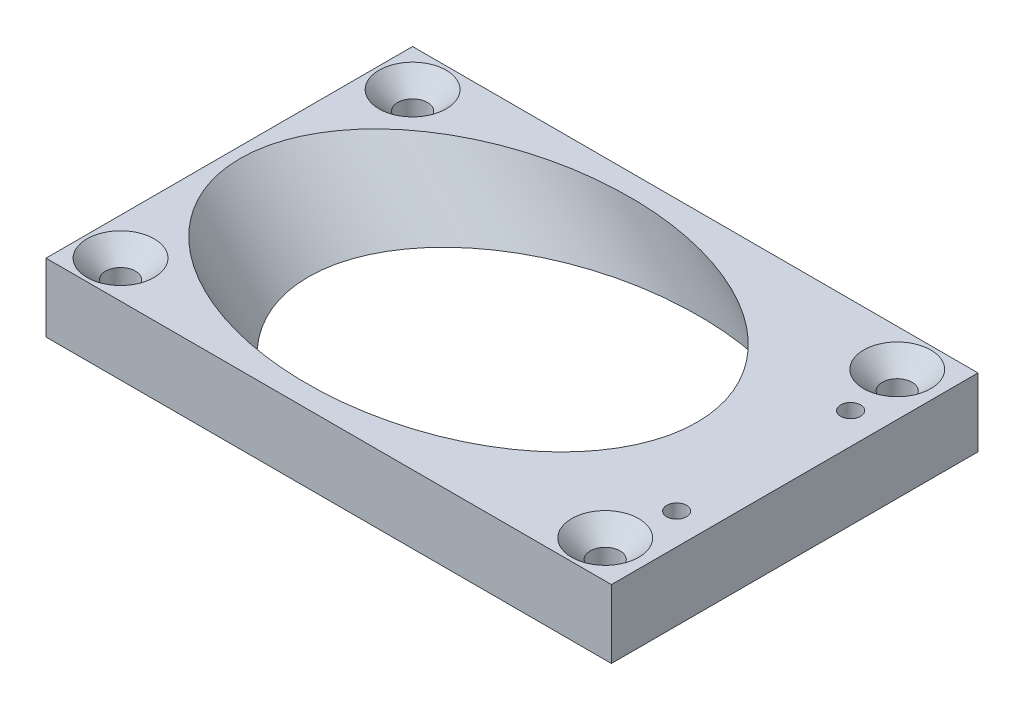
SolidWorks part; units mm, degrees
material "7075-T6 (SN)"
ref_plane "Front Plane" through (0, 0, 0) normal (0, 0, 1) x (1, 0, 0)
ref_plane "Top Plane" through (0, 0, 0) normal (0, 1, 0) x (1, 0, 0)
ref_plane "Right Plane" through (0, 0, 0) normal (1, 0, 0) x (0, 0, -1)
sketch "Sketch1" plane through (0, 0, 0) normal (0, 1, 0) x (1, 0, 0)
  line L1 (-22.75, -14.75) -> (22.75, -14.75)
  line L2 (-22.75, -14.75) -> (-22.75, 14.75)
  line L3 (-22.75, 14.75) -> (22.75, 14.75)
  line L4 (22.75, -14.75) -> (22.75, 14.75)
  line L5 (-22.75, -14.75) -> (22.75, 14.75) construction
  line L6 (-22.75, 14.75) -> (22.75, -14.75) construction
  point P0 (0, 0)
  dimension "D1" = 45.5
  dimension "D2" = 29.5
extrude "Boss-Extrude1" add sketch "Sketch1" along normal blind 5.5
ref_plane "Plane1" through (-14.125, 14.125, 0) normal (-0.7071, 0.7071, 0) x (0, 0, 1)
sketch "Sketch2" plane through (-14.125, 14.125, 0) normal (-0.7071, 0.7071, 0) x (0, 0, 1)
  line L0 (-14.75, -16.0867) -> (14.75, -16.0867) construction
  circle A0 centre (0, 1.4133) radius 13
  dimension "D1" = 26
  dimension "D2" = 17.5
extrude "Cut-Extrude1" cut sketch "Sketch2" against normal up to next
hole_wizard "CSK for M2 Countersunk Flat Head Screw1" positions "Sketch3" profile "Sketch4" countersink size "M2" standard "DIN" end condition through all
sketch "Sketch3" plane through (0, 5.5, 0) normal (0, 1, 0) x (1, 0, 0)
  line L1 (-19.75, 11.75) -> (19.25, 11.75) construction
  line L2 (-19.75, 11.75) -> (-19.75, -11.75) construction
  line L3 (-19.75, -11.75) -> (19.25, -11.75) construction
  line L4 (19.25, 11.75) -> (19.25, -11.75) construction
  line L5 (-22.75, 14.75) -> (-22.75, -14.75) construction
  line L6 (22.75, 14.75) -> (-22.75, 14.75) construction
  point P0 (-19.75, 11.75)
  point P2 (19.25, 11.75)
  point P4 (-19.75, -11.75)
  point P6 (19.25, -11.75)
  point P69 (-19.75, 0)
  dimension "D1" = 3
  dimension "D2" = 3
  dimension "D3" = 39
sketch "Sketch4" plane through (-19.75, 5.5, -11.75) normal (1, 0, 0) x (0, 0, 1)
  line L0 (0, 0) -> (0, 5.5)
  line L1 (0, 5.5) -> (1.2, 5.5)
  line L2 (1.2, 5.5) -> (1.2, 1.5)
  line L3 (1.2, 1.5) -> (2.7, 0)
  line L5 (2.7, 0) -> (0, 0)
  line L6 (-1.2, 1.5) -> (-2.7, 0) construction
  line L11 (0, -6.35) -> (0, 107.95) construction
  dimension "Thru Hole Dia." = 2.4
  dimension "Thru Hole Depth" = 5.5
  dimension "Near C'Sink Dia." = 5.4
  dimension "Near C'Sink Angle" = 90
hole_wizard "M2 Tapped Hole1" positions "Sketch5" profile "Sketch6" tap size "M2" standard "DIN" end condition through all
sketch "Sketch5" plane through (0, 5.5, 0) normal (0, 1, 0) x (1, 0, 0)
  line L0 (20.25, 7) -> (20.25, -7) construction
  line L2 (22.75, -14.75) -> (22.75, 14.75) construction
  point P0 (20.25, 7)
  point P5 (20.25, -7)
  point P13 (20.25, 0)
  dimension "D1" = 2.5
  dimension "D2" = 14
sketch "Sketch6" plane through (20.25, 5.5, -7) normal (1, 0, 0) x (0, 0, 1)
  line L0 (0, 0) -> (0, 5.5)
  line L1 (0, 5.5) -> (0.8, 5.5)
  line L2 (0.8, 5.5) -> (0.8, 0)
  line L5 (0.8, 0) -> (0, 0)
  line L11 (0, -6.35) -> (0, 107.95) construction
  dimension "Thru Tap Drill Dia." = 1.6
  dimension "Thru Tap Drill Depth" = 5.5
cosmetic thread "Hole Thread1" parameters "D2"=2
cosmetic thread "Hole Thread2" parameters "D2"=2
